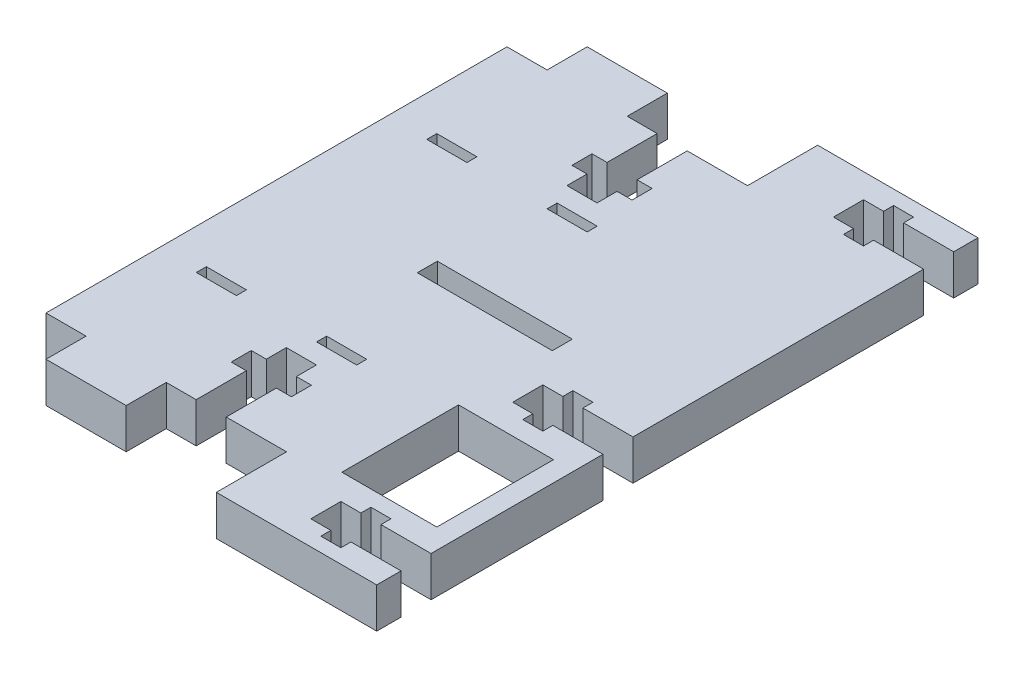
SolidWorks part; units mm, degrees
ref_plane "Front Plane" through (0, 0, 0) normal (0, 0, 1) x (1, 0, 0)
ref_plane "Top Plane" through (0, 0, 0) normal (0, 1, 0) x (1, 0, 0)
ref_plane "Right Plane" through (0, 0, 0) normal (1, 0, 0) x (0, 0, -1)
sketch "Sketch1" plane through (0, 0, 0) normal (0, 1, 0) x (1, 0, 0)
  line L0 (19.05, -19.05) -> (38.1, -19.05)
  line L1 (0, 17.4625) -> (-10.9193, 17.4625) construction
  line L2 (0, 0) -> (0, 34.925)
  line L3 (77.8648, 17.4625) -> (68.3008, 17.4625) construction
  line L4 (38.1, 0) -> (38.1, 34.925)
  line L5 (44.45, -17.4625) -> (74.6898, -17.4625)
  line L6 (38.1, 0) -> (38.1, 34.925)
  line L7 (44.45, 52.3875) -> (74.6898, 52.3875)
  line L8 (77.8648, -15.875) -> (77.8648, 50.8)
  line L9 (38.1, -30.1625) -> (84.2148, -30.1625)
  line L10 (19.05, 53.975) -> (38.1, 53.975)
  line L11 (38.1, 65.0875) -> (84.2148, 65.0875)
  line L12 (84.2148, -30.1625) -> (84.2148, 65.0875)
  line L13 (74.6898, 52.3875) -> (77.8648, 50.8)
  line L14 (77.8648, -15.875) -> (74.6898, -17.4625)
  line L15 (38.1, 0) -> (44.45, -3.6662)
  line L16 (44.45, -3.6662) -> (44.45, -17.4625)
  line L17 (38.1, 34.925) -> (44.45, 38.5912)
  line L18 (44.45, 38.5912) -> (44.45, 52.3875)
  line L21 (0, 34.925) -> (0, 53.975)
  line L22 (0, 53.975) -> (6.35, 53.975)
  line L23 (6.35, 53.975) -> (6.35, 60.325)
  line L24 (6.35, 60.325) -> (19.05, 60.325)
  line L25 (0, 0) -> (0, -19.05)
  line L26 (0, -19.05) -> (6.35, -19.05)
  line L27 (19.05, 53.975) -> (19.05, 60.325)
  line L28 (38.1, -30.1625) -> (38.1, -19.05)
  line L29 (6.35, -19.05) -> (6.35, -25.4)
  line L30 (6.35, -25.4) -> (19.05, -25.4)
  line L31 (19.05, -19.05) -> (19.05, -25.4)
  line L33 (38.1, 65.0875) -> (38.1, 53.975)
  dimension "D1" = 34.925
  dimension "D2" = 38.1
  dimension "D3" = 3.175
  dimension "D4" = 1.5875
  dimension "D5" = 69.85
  dimension "D6" = 12.7
  dimension "D7" = 12.7
  dimension "D8" = 6.35
  dimension "D10" = 1.5875
  dimension "D11" = 3.175
  dimension "D12" = 19.05
  dimension "D13" = 19.05
  dimension "D14" = 30
  dimension "D15" = 30
  dimension "D17" = 6.35
  dimension "D18" = 0
  dimension "D19" = 6.35
  dimension "D20" = 12.7
  dimension "D21" = 6.35
  dimension "D22" = 6.35
  dimension "D23" = 12.7
  dimension "D24" = 6.35
extrude "Boss-Extrude1" add sketch "Sketch1" along normal blind 6.35 contours L11 L33 L10 L27 L24 L23 L22 L21 L2 L25 L26 L29 L30 L31 L0 L28 L9 L12 L17 L18 L7 L13 L8 L14 L5 L16 L15 L4
sketch "Sketch2" plane through (0, 6.35, 0) normal (0, 1, 0) x (1, 0, 0)
  line L0 (0, -19.05) -> (0, 53.975) construction
  line L1 (6.35, 34.925) -> (12.7, 34.925)
  line L2 (6.35, 34.925) -> (6.35, 36.5125)
  line L3 (6.35, 36.5125) -> (12.7, 36.5125)
  line L4 (12.7, 34.925) -> (12.7, 36.5125)
  line L5 (6.35, 0) -> (12.7, 0)
  line L6 (6.35, 0) -> (6.35, -1.5875)
  line L7 (6.35, -1.5875) -> (12.7, -1.5875)
  line L8 (12.7, 0) -> (12.7, -1.5875)
  line L9 (25.4, 34.925) -> (31.75, 34.925)
  line L10 (25.4, 34.925) -> (25.4, 36.5125)
  line L11 (25.4, 36.5125) -> (31.75, 36.5125)
  line L12 (31.75, 34.925) -> (31.75, 36.5125)
  line L13 (25.4, 0) -> (31.75, 0)
  line L14 (25.4, 0) -> (25.4, -1.5875)
  line L15 (25.4, -1.5875) -> (31.75, -1.5875)
  line L16 (31.75, 0) -> (31.75, -1.5875)
  dimension "D1" = 6.35
  dimension "D2" = 6.35
  dimension "D3" = 12.7
  dimension "D4" = 6.35
  dimension "D5" = 6.35
  dimension "D6" = 6.35
  dimension "D7" = 12.7
  dimension "D8" = 6.35
  dimension "D9" = 1.5875
  dimension "D10" = 1.5875
  dimension "D11" = 1.5875
  dimension "D12" = 1.5875
  dimension "D13" = 0
  dimension "D14" = 0
extrude "Cut-Extrude1" cut sketch "Sketch2" against normal blind 6.35
sketch "Sketch3" plane through (0, 6.35, 0) normal (0, 1, 0) x (1, 0, 0)
  line L0 (19.05, 53.975) -> (38.1, 53.975) construction
  line L1 (23.787, 53.975) -> (28.5495, 53.975)
  line L2 (23.787, 53.975) -> (23.787, 39.6875)
  line L3 (23.787, 39.6875) -> (28.5495, 39.6875)
  line L4 (28.5495, 53.975) -> (28.5495, 39.6875)
  line L5 (84.2148, -30.1625) -> (84.2148, 65.0875) construction
  line L6 (21.4058, 46.0375) -> (30.9308, 46.0375)
  line L7 (21.4058, 46.0375) -> (21.4058, 42.8625)
  line L8 (21.4058, 42.8625) -> (30.9308, 42.8625)
  line L9 (30.9308, 46.0375) -> (30.9308, 42.8625)
  line L10 (84.2148, 60.4838) -> (69.9273, 60.4838)
  line L11 (84.2148, 60.4838) -> (84.2148, 55.7213)
  line L12 (84.2148, 55.7213) -> (69.9273, 55.7213)
  line L13 (69.9273, 60.4838) -> (69.9273, 55.7213)
  line L14 (76.2773, -27.1463) -> (76.2773, -19.2088)
  line L15 (73.1023, 62.0713) -> (76.2773, 62.0713)
  line L16 (73.1023, 62.0713) -> (73.1023, 54.1338)
  line L17 (73.1023, 54.1338) -> (76.2773, 54.1338)
  line L18 (76.2773, 62.0713) -> (76.2773, 54.1338)
  line L19 (38.1, 17.4625) -> (77.8648, 17.4625) construction
  line L20 (38.1, 0) -> (38.1, 34.925) construction
  line L21 (77.8648, -15.875) -> (77.8648, 50.8) construction
  line L22 (69.9273, 58.1025) -> (57.9922, 58.1025) construction
  line L23 (73.1023, -19.2088) -> (76.2773, -19.2088)
  line L24 (73.1023, -27.1463) -> (73.1023, -19.2088)
  line L25 (73.1023, -27.1463) -> (76.2773, -27.1463)
  line L26 (69.9273, -25.5588) -> (69.9273, -20.7963)
  line L27 (84.2148, -20.7962) -> (69.9273, -20.7963)
  line L28 (84.2148, -25.5587) -> (84.2148, -20.7962)
  line L29 (84.2148, -25.5587) -> (69.9273, -25.5588)
  line L30 (30.9308, -11.1125) -> (30.9308, -7.9375)
  line L31 (21.4058, -7.9375) -> (30.9308, -7.9375)
  line L32 (21.4058, -11.1125) -> (21.4058, -7.9375)
  line L33 (21.4058, -11.1125) -> (30.9308, -11.1125)
  line L34 (28.5495, -19.05) -> (28.5495, -4.7625)
  line L35 (23.787, -4.7625) -> (28.5495, -4.7625)
  line L36 (23.787, -19.05) -> (23.787, -4.7625)
  line L37 (23.787, -19.05) -> (28.5495, -19.05)
  dimension "D1" = 4.7625
  dimension "D2" = 9.525
  dimension "D3" = 2.3813
  dimension "D4" = 7.9375
  dimension "D5" = 3.175
  dimension "D6" = 3.175
  dimension "D7" = 4.7625
  dimension "D8" = 7.9375
  dimension "D9" = 1.5875
  dimension "D10" = 7.9375
  dimension "D11" = 3.175
  dimension "D12" = 3.175
  dimension "D13" = 40.64
sketch "Sketch4" plane through (0, 6.35, 0) normal (0, 1, 0) x (1, 0, 0)
  line L0 (61.9898, 52.3875) -> (61.9898, -17.4625)
  line L1 (44.45, 52.3875) -> (74.6898, 52.3875) construction
  line L2 (44.45, -17.4625) -> (74.6898, -17.4625) construction
  line L3 (77.8648, -15.875) -> (77.8648, 50.8) construction
  line L4 (61.9898, 52.3875) -> (37.6631, 52.3875)
  line L5 (37.6631, 52.3875) -> (37.6631, -17.4625)
  line L6 (37.6631, -17.4625) -> (61.9898, -17.4625)
  dimension "D1" = 15.875
extrude "Boss-Extrude2" add sketch "Sketch4" along normal blind 6.35 from surface at -6.35 starting at plane "Top Plane"
sketch "Sketch5" plane through (0, 6.35, 0) normal (0, 1, 0) x (1, 0, 0)
  line L0 (61.9898, -17.4625) -> (61.9898, 52.3875) construction
  line L1 (74.6898, 15.875) -> (49.2898, 15.875)
  line L2 (74.6898, 15.875) -> (74.6898, 19.05)
  line L3 (74.6898, 19.05) -> (49.2898, 19.05)
  line L4 (49.2898, 15.875) -> (49.2898, 19.05)
  line L5 (74.6898, 15.875) -> (49.2898, 19.05) construction
  line L6 (74.6898, 19.05) -> (49.2898, 15.875) construction
  line L8 (49.2898, 19.05) -> (23.8898, 19.05)
  line L9 (49.2898, 19.05) -> (49.2898, 15.875)
  line L10 (49.2898, 15.875) -> (23.8898, 15.875)
  line L11 (23.8898, 19.05) -> (23.8898, 15.875)
  point P0 (61.9898, 17.4625)
  dimension "D1" = 3.175
  dimension "D2" = 25.4
  dimension "D3" = 25.4
extrude "Cut-Extrude3" cut sketch "Sketch5" against normal blind 6.35 contours L4 L1 L2 L3 | L8 L11 L10 L4
sketch "Sketch7" plane through (0, 6.35, 0) normal (0, 1, 0) x (1, 0, 0)
  line L0 (38.1, -30.1625) -> (84.2148, -30.1625) construction
  line L1 (81.0398, -30.1625) -> (100.9634, -30.1625)
  line L2 (81.0398, -30.1625) -> (81.0398, 65.0875)
  line L3 (81.0398, 65.0875) -> (100.9634, 65.0875)
  line L4 (100.9634, -30.1625) -> (100.9634, 65.0875)
  line L5 (77.8648, -15.875) -> (77.8648, 50.8) construction
  dimension "D1" = 3.175
extrude "Cut-Extrude4" cut sketch "Sketch7" against normal blind 6.35
sketch "Sketch8" plane through (0, 0, 0) normal (0, -1, 0) x (1, 0, 0)
  line L0 (61.9898, -52.3875) -> (74.6898, -52.3875) construction
  line L1 (45.2817, 17.4625) -> (60.325, 17.4625)
  line L2 (45.2817, 17.4625) -> (45.2817, -52.3875)
  line L3 (45.2817, -52.3875) -> (60.325, -52.3875)
  line L4 (60.325, 17.4625) -> (60.325, -52.3875)
  line L5 (38.1, 30.1625) -> (38.1, 19.05) construction
  dimension "D1" = 22.225
extrude "Cut-Extrude5" cut sketch "Sketch8" against normal blind 6.35
sketch "Sketch9" plane through (0, 0, 0) normal (0, -1, 0) x (1, 0, 0)
  line L0 (38.1, 30.1625) -> (81.0398, 30.1625) construction
  line L1 (60.325, 30.1625) -> (63.5, 30.1625)
  line L2 (60.325, 30.1625) -> (60.325, -65.0875)
  line L3 (60.325, -65.0875) -> (63.5, -65.0875)
  line L4 (63.5, 30.1625) -> (63.5, -65.0875)
  line L5 (38.1, -65.0875) -> (81.0398, -65.0875) construction
  dimension "D1" = 3.175
extrude "Boss-Extrude3" add sketch "Sketch9" against normal blind 6.35 from surface at 0 starting at plane "Top Plane"
sketch "Sketch10" plane through (0, 0, 0) normal (0, -1, 0) x (1, 0, 0)
  line L0 (38.1, 30.1625) -> (81.0398, 30.1625) construction
  line L1 (63.5, 30.1625) -> (81.0398, 30.1625)
  line L2 (63.5, 30.1625) -> (63.5, -65.0875)
  line L3 (63.5, -65.0875) -> (81.0398, -65.0875)
  line L4 (81.0398, 30.1625) -> (81.0398, -65.0875)
  line L5 (38.1, -65.0875) -> (81.0398, -65.0875) construction
extrude "Cut-Extrude7" cut sketch "Sketch10" against normal blind 6.35
extrude "Cut-Extrude8" cut sketch "Sketch3" against normal blind 6.35 contours L4 L3 L2 L1 | L6 L9 L8 L7 | L34 L35 L36 L37 | L31 L30 L33 L32
sketch "Sketch11" plane through (0, 0, 0) normal (0, -1, 0) x (1, 0, 0)
  line L0 (63.5, -65.0875) -> (63.5, 30.1625) construction
  line L1 (63.5, 26.3133) -> (49.2125, 26.3133)
  line L2 (63.5, 26.3133) -> (63.5, 21.5508)
  line L3 (63.5, 21.5508) -> (49.2125, 21.5508)
  line L4 (49.2125, 26.3133) -> (49.2125, 21.5508)
  line L5 (60.325, -52.3875) -> (60.325, 17.4625) construction
  line L6 (52.3875, 27.9008) -> (55.5625, 27.9008)
  line L7 (52.3875, 27.9008) -> (52.3875, 19.9633)
  line L8 (52.3875, 19.9633) -> (55.5625, 19.9633)
  line L9 (55.5625, 27.9008) -> (55.5625, 19.9633)
  line L10 (60.325, -17.4625) -> (54.7157, -17.4625)
  line L11 (60.325, -17.4625) -> (60.325, -17.3657)
  line L12 (60.325, -17.3657) -> (54.7157, -17.3657)
  line L13 (54.7157, -17.4625) -> (54.7157, -17.3657)
  line L14 (55.5625, -62.8258) -> (55.5625, -54.8883)
  line L15 (52.3875, -54.8883) -> (55.5625, -54.8883)
  line L16 (52.3875, -62.8258) -> (52.3875, -54.8883)
  line L17 (52.3875, -62.8258) -> (55.5625, -62.8258)
  line L18 (49.2125, -61.2383) -> (49.2125, -56.4758)
  line L19 (63.5, -56.4758) -> (49.2125, -56.4758)
  line L20 (63.5, -61.2383) -> (63.5, -56.4758)
  line L21 (63.5, -61.2383) -> (49.2125, -61.2383)
  dimension "D1" = 4.7625
  dimension "D2" = 7.9375
  dimension "D3" = 1.5875
  dimension "D4" = 7.9375
  dimension "D5" = 3.175
  dimension "D6" = 3.175
extrude "Cut-Extrude9" cut sketch "Sketch11" against normal blind 6.35 contours L1 L4 L3 L2 | L6 L9 L8 L7 | L18 L19 L20 L21 | L15 L14 L17 L16
sketch "Sketch13" plane through (0, 0, 0) normal (0, -1, 0) x (1, 0, 0)
  line L0 (45.2817, 17.4625) -> (45.2817, -15.875) construction
  line L1 (45.2817, -1.0183) -> (60.325, -1.0183)
  line L2 (45.2817, -1.0183) -> (45.2817, -52.3875)
  line L3 (45.2817, -52.3875) -> (60.325, -52.3875)
  line L4 (60.325, -1.0183) -> (60.325, -52.3875)
  line L5 (60.325, -52.3875) -> (60.325, 17.4625) construction
extrude "Boss-Extrude4" add sketch "Sketch13" against normal blind 6.35
sketch "Sketch14" plane through (0, 0, 0) normal (0, -1, 0) x (1, 0, 0)
  line L0 (63.5, -56.4758) -> (63.5, 21.5508) construction
  line L1 (63.5, -10.4383) -> (49.2125, -10.4383)
  line L2 (63.5, -10.4383) -> (63.5, -5.6758)
  line L3 (63.5, -5.6758) -> (49.2125, -5.6758)
  line L4 (49.2125, -10.4383) -> (49.2125, -5.6758)
  line L5 (63.5, -61.2383) -> (55.5625, -61.2383) construction
  line L6 (52.3875, -4.0883) -> (55.5625, -4.0883)
  line L7 (52.3875, -4.0883) -> (52.3875, -12.0258)
  line L8 (52.3875, -12.0258) -> (55.5625, -12.0258)
  line L9 (55.5625, -4.0883) -> (55.5625, -12.0258)
  dimension "D1" = 4.7625
  dimension "D2" = 7.9375
  dimension "D3" = 1.5875
  dimension "D4" = 7.9375
  dimension "D5" = 3.175
  dimension "D6" = 3.175
  dimension "D7" = 50.8
extrude "Cut-Extrude10" cut sketch "Sketch14" against normal blind 6.35 contours L3 L4 L1 L2 | L7 L8 L9 L6
